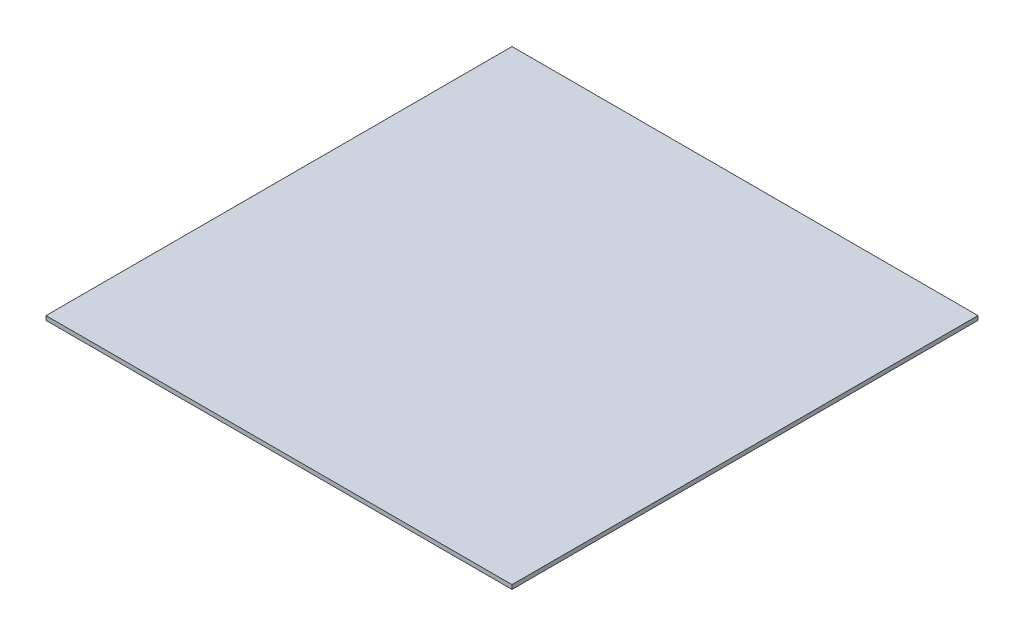
SolidWorks part; units mm, degrees
ref_plane "Front Plane" through (0, 0, 0) normal (0, 0, 1) x (1, 0, 0)
ref_plane "Top Plane" through (0, 0, 0) normal (0, 1, 0) x (1, 0, 0)
ref_plane "Right Plane" through (0, 0, 0) normal (1, 0, 0) x (0, 0, -1)
sketch "Sketch1" plane through (0, 0, 0) normal (0, 1, 0) x (1, 0, 0)
  line L1 (-250, 250) -> (250, 250)
  line L2 (-250, 250) -> (-250, -250)
  line L3 (-250, -250) -> (250, -250)
  line L4 (250, 250) -> (250, -250)
  line L5 (-250, 250) -> (250, -250) construction
  line L6 (-250, -250) -> (250, 250) construction
  point P0 (0, 0)
  dimension "D1" = 500
  dimension "D2" = 500
extrude "Boss-Extrude1" add sketch "Sketch1" along normal blind 4.5
